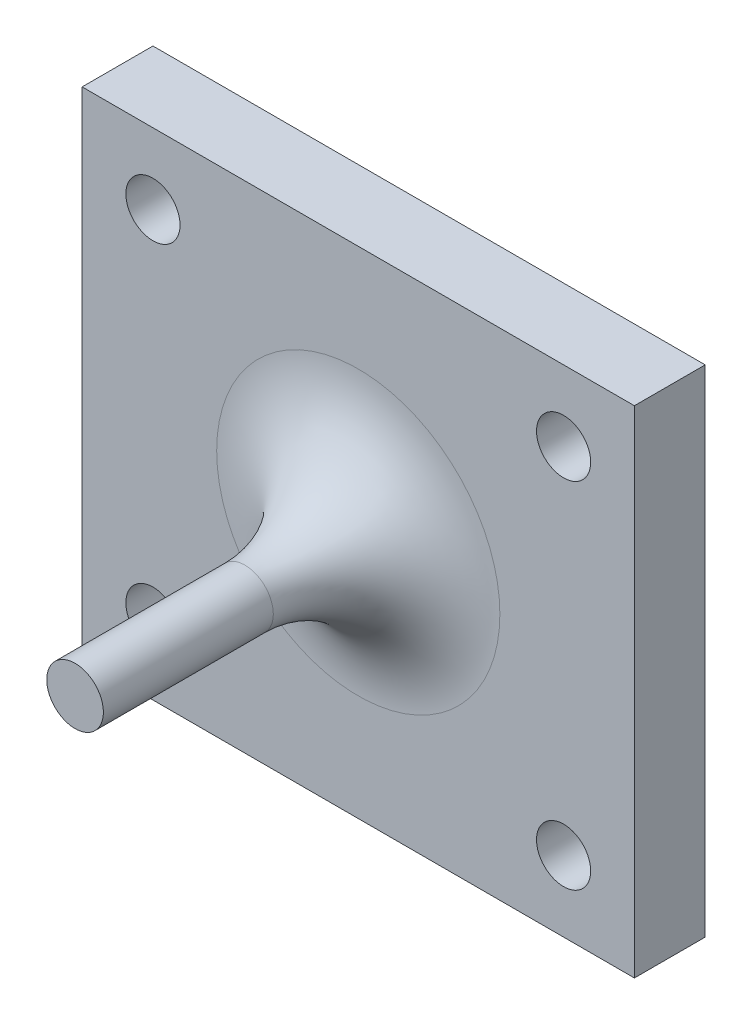
SolidWorks part; units mm, degrees
ref_plane "Front Plane" through (0, 0, 0) normal (0, 0, 1) x (1, 0, 0)
ref_plane "Top Plane" through (0, 0, 0) normal (0, 1, 0) x (1, 0, 0)
ref_plane "Right Plane" through (0, 0, 0) normal (1, 0, 0) x (0, 0, -1)
sketch "Sketch1" plane through (0, 0, 0) normal (0, 0, 1) x (1, 0, 0)
  line L0 (17.5, 17.5) -> (-17.5, 17.5) construction
  line L1 (-19.5, 17.5) -> (19.5, 17.5)
  line L2 (-19.5, 17.5) -> (-19.5, -17.5)
  line L3 (-19.5, -17.5) -> (19.5, -17.5)
  line L4 (19.5, 17.5) -> (19.5, -17.5)
  line L5 (-19.5, 15.5) -> (-19.5, -15.5) construction
  line L6 (19.5, -15.5) -> (19.5, 15.5) construction
  line L7 (-17.5, -17.5) -> (17.5, -17.5) construction
  circle A0 centre (14.5, -12.5) radius 1.9127 construction
  circle A1 centre (14.5, 12.5) radius 1.9127 construction
  circle A2 centre (-14.5, -12.5) radius 1.9127 construction
  circle A3 centre (-14.5, 12.5) radius 1.9127 construction
  circle A4 centre (14.5, -12.5) radius 1.9127
  circle A5 centre (14.5, 12.5) radius 1.9127
  circle A6 centre (-14.5, -12.5) radius 1.9127
  circle A7 centre (-14.5, 12.5) radius 1.9127
  point P16 (-18.2625, 17.8013)
  point P17 (-19.6132, 17.6478)
extrude "Boss-Extrude1" add sketch "Sketch1" along normal blind 5
sketch "Sketch2" plane through (0, 0, 5) normal (0, 0, 1) x (1, 0, 0)
  line L0 (-19.5, 17.5) -> (19.5, -17.5) construction
  line L1 (19.5, 17.5) -> (-19.5, -17.5) construction
  circle A0 centre (0, 0) radius 2
  dimension "D1" = 4
extrude "Boss-Extrude2" add sketch "Sketch2" along normal blind 20
fillet "Fillet1" radius 8 1 edges at (2, 0, 5)
